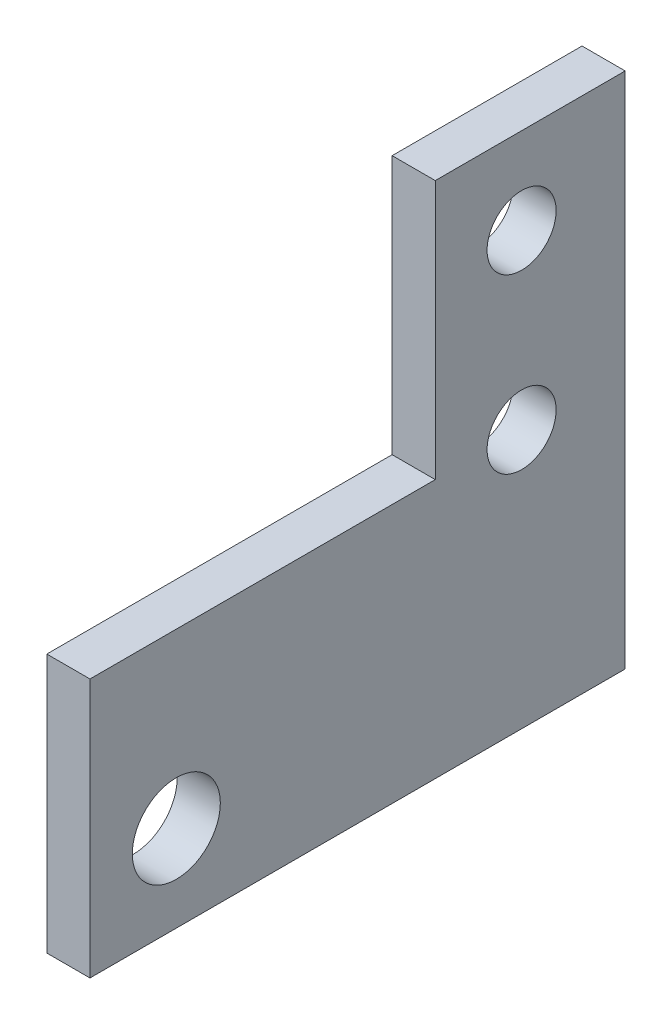
SolidWorks part; units mm, degrees
ref_plane "Front Plane" through (0, 0, 0) normal (0, 0, 1) x (1, 0, 0)
ref_plane "Top Plane" through (0, 0, 0) normal (0, 1, 0) x (1, 0, 0)
ref_plane "Right Plane" through (0, 0, 0) normal (1, 0, 0) x (0, 0, -1)
sketch "Sketch2" plane through (0, 0, 0) normal (1, 0, 0) x (0, 0, -1)
  line L0 (52, -10) -> (52, 50)
  line L3 (52, 50) -> (30, 50)
  line L6 (30, 50) -> (30, 20)
  line L7 (30, 20) -> (-10, 20)
  line L8 (-10, 20) -> (-10, -10)
  line L9 (-10, -10) -> (52, -10)
  circle A0 centre (40, 40) radius 4
  circle A1 centre (40, 20) radius 4
  circle A2 centre (0, 0) radius 5.1
  dimension "D3" = 8
  dimension "D7" = 8
  dimension "D11" = 10.2
  dimension "D2" = 30
  dimension "D4" = 12
  dimension "D5" = 10
  dimension "D6" = 22
  dimension "D8" = 20
  dimension "D9" = 40
  dimension "D10" = 12
  dimension "D13" = 60
  dimension "D15" = 20
  dimension "D16" = 40
extrude "Boss-Extrude3" add sketch "Sketch2" along normal blind 5
